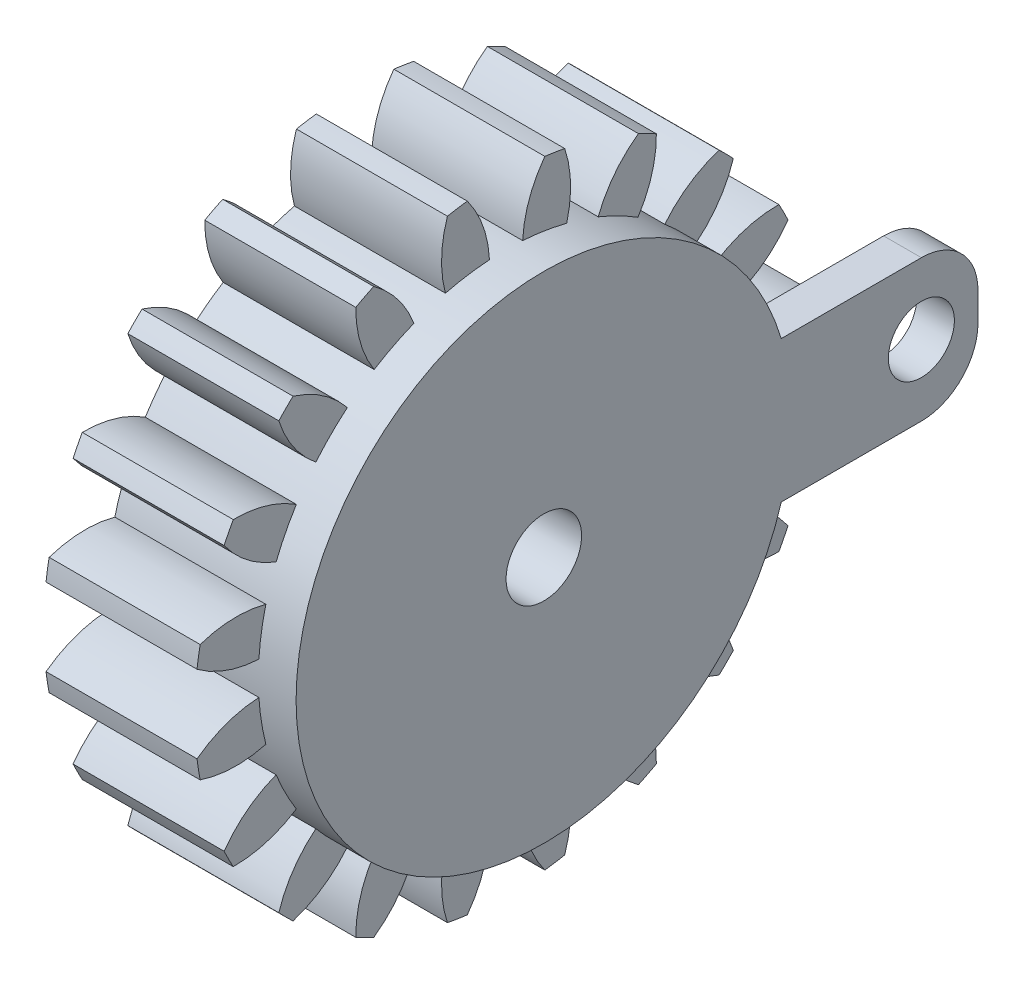
SolidWorks part; units mm, degrees
ref_plane "Plane1" through (0, 0, 0) normal (0, 0, 1) x (1, 0, 0)
ref_plane "Plane2" through (0, 0, 0) normal (0, 1, 0) x (1, 0, 0)
ref_plane "Plane3" through (0, 0, 0) normal (1, 0, 0) x (0, 0, -1)
other "Configuration Table"
sketch "HoldingSke" plane through (0, 0, 0) normal (0, 1, 0) x (1, 0, 0)
  line L0 (0, 0) -> (0.6265, -0.228)
  line L1 (-15, 0) -> (100, 0) construction
  line L2 (0, 0) -> (-2.1039, 2.3779)
  line L3 (0, 0) -> (-11.863, 4.5341)
  line L4 (0, 0) -> (8.1152, 2.9537)
  line L5 (0, 0) -> (-46.8476, -17.4728)
  line L6 (0, 0) -> (-6.6317, -4.4744)
  line L7 (-2.1039, 2.3779) -> (8.6586, 51.2059)
  line L8 (-76.2, 54.61) -> (-75.5, 54.61)
  line L9 (-67.7845, 28.3722) -> (-49.3413, 33.142)
  line L10 (-76.2, 71.12) -> (104.1128, 71.12)
  line L11 (0, 0) -> (-8, 0)
  line L12 (-76.2, 101.6) -> (-76.147, 101.6)
  line L13 (24.9733, 27.94) -> (52.9518, 28.4284)
  line L14 (24.9733, 27.94) -> (24.9743, 27.94)
  line L15 (24.9733, 27.94) -> (100.4006, 29.5858)
  line L16 (-63.627, -1.5) -> (-12.827, -1.5)
  circle A0 centre (0, 0) radius 2
  circle A1 centre (0, 0) radius 13.124
  circle A2 centre (0, 0) radius 37.5
  circle A3 centre (0, 0) radius 2
  dimension "MHD" = 26.248
  dimension "Hub_dia" = 75
  dimension "Bore" = 4
  dimension "MBD" = 4
  dimension "Num_teeth" = 20
  dimension "Pitch" = 0.6667
  dimension "Overall_len" = 50
  dimension "Show_teeth" = 20
  dimension "Thickness" = 8
  dimension "OAL" = 50.0001
  dimension "T_dim" = 0.7
  dimension "Ap" = 14.5
  dimension "H" = 19.05
  dimension "Pitch_radius" = 180.3128
  dimension "Width" = 8
  dimension "Backlash" = 0.053
  dimension "Addendum_fac" = 1
  dimension "Dedendum_fac" = 1.25
  dimension "Clearance_fac" = 0.25
  dimension "Dedendum_add" = 0.001
  dimension "Module" = 1.5
sketch "BasProSke" plane through (0, 0, 0) normal (0, 1, 0) x (1, 0, 0)
  line L0 (-10, 0) -> (60, 0) construction
  line L1 (0, 0) -> (0, 16.5)
  line L2 (0, 0) -> (8, 0)
  line L3 (8, 0) -> (8, 16.5)
  line L4 (8, 16.5) -> (0, 16.5)
  dimension "Thickness" = 8
  dimension "Diameter" = 33
revolve "Base-Revolve" add sketch "BasProSke" angle 360 about L0
sketch "TooCutSke" plane through (0, 0, 0) normal (1, 0, 0) x (0, 0, -1)
  line L1 (0, 0) -> (0, 107) construction
  line L2 (0, 0) -> (-1.2696, 14.9462) construction
  line L3 (0, 0) -> (-4.6808, 29.5532) construction
  line L4 (-1.2696, 14.9462) -> (-2.3404, 14.7766) construction
  arc A0 (0.8779, 13.0946) -> (-0.8779, 13.0946) centre (0, 0) ccw
  arc A1 (2.0711, 16.3951) -> (-2.0711, 16.3951) centre (0, 0) ccw
  circle A2 centre (0, 0) radius 15 construction
  circle A3 centre (0, 0) radius 14.5222 construction
  arc A4 (-0.8779, 13.0946) -> (-2.0711, 16.3951) centre (-6.8704, 12.7942) ccw
  arc A5 (2.0711, 16.3951) -> (0.8779, 13.0946) centre (6.8704, 12.7942) ccw
  dimension "Root_dia" = 26.248
  dimension "Overcut_dia" = 33.0508
  dimension "Pitch_dia" = 30
  dimension "Base_dia" = 29.0444
  dimension "Flank_rad" = 6
  dimension "Half_ang" = 9
  dimension "Half_CT" = 1.0841
extrude "ToothCut" cut sketch "TooCutSke" along normal through all
fillet "Breaks" [suppressed] radius 0.03
fillet "RootFillets" [suppressed] radius 0.376
pattern_circular "TeethCuts" count 20 every 18 about axis through (-10, 0, 0) along (1, 0, 0) of "ToothCut", "RootFillets", "Breaks"
sketch "HubNeaOneSke" plane through (0, 0, 0) normal (-1, 0, 0) x (0, 0, 1)
  circle A0 centre (0, 0) radius 13.124
  dimension "Diameter" = 26.248
extrude "HubNearOne" [suppressed] add sketch "HubNeaOneSke" along normal blind 42.0001
sketch "HubNeaBotSke" plane through (0, 0, 0) normal (-1, 0, 0) x (0, 0, 1)
  circle A0 centre (0, 0) radius 13.124
  dimension "Diameter" = 26.248
extrude "HubNearBoth" [suppressed] add sketch "HubNeaBotSke" along normal blind 21
ref_plane "FarPln" through (8, 0, 0) normal (1, 0, 0) x (0, 0, -1)
sketch "HubFarSke" plane through (8, 0, 0) normal (1, 0, 0) x (0, 0, -1)
  circle A0 centre (0, 0) radius 13.124
  dimension "Diameter" = 26.248
extrude "HubFar" [suppressed] add sketch "HubFarSke" along normal blind 21
sketch "BorSke" plane through (0, 0, 0) normal (1, 0, 0) x (0, 0, -1)
  circle A0 centre (0, 0) radius 2
  dimension "Diameter" = 4
extrude "Bore" cut sketch "BorSke" along normal mid plane 100.0001
sketch "KeySke" plane through (0, 0, 0) normal (1, 0, 0) x (0, 0, -1)
  line L0 (-0.8, 0) -> (-0.8, 2.7)
  line L1 (-0.8, 2.7) -> (0.8, 2.7)
  line L2 (0.8, 2.7) -> (0.8, 0)
  line L3 (0, 0) -> (0, 34) construction
  line L4 (-0.8, 0) -> (0.8, 0)
  dimension "Offset" = 2.7
  dimension "Width" = 1.6
extrude "Keyway" [suppressed] cut sketch "KeySke" along normal mid plane 100.0001
pattern_circular "Keyway2" [suppressed] count 2 every 90 about axis through (-10, 0, 0) along (1, 0, 0)
sketch "Sketch1" plane through (8, 0, 0) normal (1, 0, 0) x (0, 0, -1)
  line L0 (0, 0) -> (0, 3.75)
  line L1 (0, 3.75) -> (20, 3.75)
  line L2 (20, 3.75) -> (23, 3.75)
  line L3 (23, 3.75) -> (23, -3.75)
  line L4 (23, -3.75) -> (0, -3.75)
  line L5 (0, -3.75) -> (0, 0)
  circle A0 centre (20, 0) radius 1.75
extrude "Boss-Extrude1" add sketch "Sketch1" along normal blind 2
sketch "Sketch2" plane through (8, 0, 0) normal (1, 0, 0) x (0, 0, -1)
  line L1 (23, 3.75) -> (0, 3.75) construction
  line L2 (12.5768, -3.75) -> (0, -3.75)
  line L3 (0, -3.75) -> (0, 3.75)
  line L4 (0, 3.75) -> (12.5768, 3.75)
  line L5 (0, -3.75) -> (23, -3.75) construction
  arc A3 (12.5768, 3.75) -> (12.5768, -3.75) centre (0, 0) ccw
extrude "Boss-Extrude2" add sketch "Sketch2" along normal blind 2 contours L4 A3 L2 L3
sketch "Sketch3" plane through (0, 0, 0) normal (-1, 0, 0) x (0, 0, 1)
  circle A0 centre (0, 0) radius 2
extrude "Cut-Extrude1" cut sketch "Sketch3" against normal blind 15
fillet "Fillet1" radius 3 2 edges at (9, -3.75, -23) (9, 3.75, -23)
equation "' \"Module@HoldingSke\" = 6.35"
equation "' \"Num_teeth@HoldingSke\" = 12"
equation "' \"Ap@HoldingSke\" =  20"
equation "' \"Ap@HoldingSke\" = 20"
equation "' \"Width@HoldingSke\" = 0.5 * 25.4"
equation "' \"Hub_dia@HoldingSke\"= 1 * 25.4"
equation "' \"Hub_dia@HoldingSke\" = 1 * 25.4"
equation "' \"Overall_len@HoldingSke\" = 1.0 * 25.4"
equation "' \"Bore@HoldingSke\" = 0.75 * 25.4"
equation "' \"T_dim@HoldingSke\" = 0.1 * 25.4"
equation "' \"Width@KeySke\" = 0.25 * 25.4"
equation "' \"Show_teeth@HoldingSke\" = 13"
equation "' \"Backlash@HoldingSke\" = 0.009 * 25.4"
equation "' \"Addendum_fac@HoldingSke\" = 1.0"
equation "' \"Dedendum_fac@HoldingSke\" = 1.25"
equation "' \"Dedendum_add@HoldingSke\" = 0.00005 * 25.4"
equation "' \"Clearance_fac@HoldingSke\" = 0.25"
equation "\"Pitch@HoldingSke\" = 1 / \"Module@HoldingSke\""
equation "\"Overcut_dia@TooCutSke\" = (\"Num_teeth@HoldingSke\" + 2 * \"Addendum_fac@HoldingSke\") / \"Pitch@HoldingSke\" + 0.002 * 25.4"
equation "\"Pitch_dia@TooCutSke\" = \"Num_teeth@HoldingSke\" / \"Pitch@HoldingSke\""
equation "\"Base_dia@TooCutSke\" = \"Num_teeth@HoldingSke\" / \"Pitch@HoldingSke\" * cos((\"Ap@HoldingSke\"  * 3.14159265 / 180))"
equation "\"Root_dia@TooCutSke\" = (\"Num_teeth@HoldingSke\" + 2) / \"Pitch@HoldingSke\" - 2 * (\"Addendum_fac@HoldingSke\" + \"Dedendum_fac@HoldingSke\") / \"Pitch@HoldingSke\" - \"Dedendum_add@HoldingSke\" * 2"
equation "\"Half_ang@TooCutSke\" = 180 / \"Num_teeth@HoldingSke\""
equation "\"Half_CT@TooCutSke\" = \"Num_teeth@HoldingSke\" / \"Pitch@HoldingSke\" * sin((3.14159265 / 2 / \"Num_teeth@HoldingSke\")) / 2 - 7 * \"Backlash@HoldingSke\" / 4"
equation "\"Flank_rad@TooCutSke\" = \"Num_teeth@HoldingSke\" / \"Pitch@HoldingSke\" / 5"
equation "\"Radius@RootFillets\" = \"Clearance_fac@HoldingSke\" / \"Pitch@HoldingSke\" + \"Dedendum_add@HoldingSke\""
equation "\"Break_rad@Breaks\" = 0.02 / \"Pitch@HoldingSke\""
equation "\"Thickness@HoldingSke\" = \"Width@HoldingSke\""
equation "\"OAL@HoldingSke\" = \"Thickness@HoldingSke\""
equation "\"MHD@HoldingSke\" = (\"Num_teeth@HoldingSke\" + 2) / \"Pitch@HoldingSke\" - 2 * (\"Addendum_fac@HoldingSke\" + \"Dedendum_fac@HoldingSke\")  / \"Pitch@HoldingSke\" - \"Dedendum_add@HoldingSke\" * 2"
equation "\"MBD@HoldingSke\" = (\"Num_teeth@HoldingSke\" + 2) / \"Pitch@HoldingSke\" - 2 * (\"Addendum_fac@HoldingSke\" + \"Dedendum_fac@HoldingSke\")  / \"Pitch@HoldingSke\" - \"Dedendum_add@HoldingSke\" * 2 - 0.002 * 25.4"
equation "\"MHD@HoldingSke\" = ((sgn( \"MHD@HoldingSke\" - \"Hub_dia@HoldingSke\" )-1)*( \"MHD@HoldingSke\" - \"Hub_dia@HoldingSke\" ))/-2+ \"Hub_dia@HoldingSke\""
equation "\"MBD@HoldingSke\" = ((sgn( \"MBD@HoldingSke\" - \"Bore@HoldingSke\" )-1)*( \"MBD@HoldingSke\" - \"Bore@HoldingSke\" ))/-2+ \"Bore@HoldingSke\""
equation "\"OAL@HoldingSke\" = ((sgn( \"OAL@HoldingSke\" - \"Overall_len@HoldingSke\" )+1)*( \"OAL@HoldingSke\" - \"Overall_len@HoldingSke\" ))/2 + \"Overall_len@HoldingSke\" + 0.000002 * 25.4"
equation "\"Num_teeth@TeethCuts\" = int( \"Show_teeth@HoldingSke\" ) + 1"
equation "\"Num_teeth@TeethCuts\" = ((sgn( \"Num_teeth@TeethCuts\" - \"Num_teeth@HoldingSke\" )-1)*( \"Num_teeth@TeethCuts\" - \"Num_teeth@HoldingSke\" ))/-2+ \"Num_teeth@HoldingSke\""
equation "\"Num_teeth@TeethCuts\" = ((sgn( \"Num_teeth@TeethCuts\" - 2.0)+1)*( \"Num_teeth@TeethCuts\" - 2.0))/2 +2.0"
equation "\"Angle@TeethCuts\" = 360.0 / \"Num_teeth@HoldingSke\""
equation "\"Diameter@BasProSke\" = (\"Num_teeth@HoldingSke\" + 2 * \"Addendum_fac@HoldingSke\") / \"Pitch@HoldingSke\""
equation "\"Thickness@BasProSke\"  = \"Thickness@HoldingSke\""
equation "' \"Fillet_rad@BasProSke\" =  \"Thickness@HoldingSke\" * 0.05"
equation "' \"Fillet_rad@BasProSke\" = \"Thickness@HoldingSke\" * 0.05"
equation "\"MHD@HoldingSke\" = ((sgn( \"MHD@HoldingSke\" - \"Root_dia@TooCutSke\" )-1)*( \"MHD@HoldingSke\" - \"Root_dia@TooCutSke\" ))/-2+ \"Root_dia@TooCutSke\""
equation "\"Diameter@HubNeaOneSke\" = \"MHD@HoldingSke\""
equation "\"Length@HubNearOne\" = \"OAL@HoldingSke\" - \"Thickness@BasProSke\""
equation "\"Diameter@HubNeaBotSke\" = \"MHD@HoldingSke\""
equation "\"Length@HubNearBoth\" = ( \"OAL@HoldingSke\" - \"Thickness@BasProSke\" ) / 2.0"
equation "\"Thickness@FarPln\" = \"Thickness@BasProSke\""
equation "\"Diameter@HubFarSke\" = \"MHD@HoldingSke\""
equation "\"Length@HubFar\" = ( \"OAL@HoldingSke\" - \"Thickness@BasProSke\" ) / 2.0"
equation "\"Diameter@BorSke\" = \"MBD@HoldingSke\""
equation "\"D1@Bore\" = \"OAL@HoldingSke\" * 2.0"
equation "\"D1@Keyway\" = \"OAL@HoldingSke\" * 2.0"
equation "\"Offset@KeySke\" = \"T_dim@HoldingSke\" + \"MBD@HoldingSke\" / 2.0"
